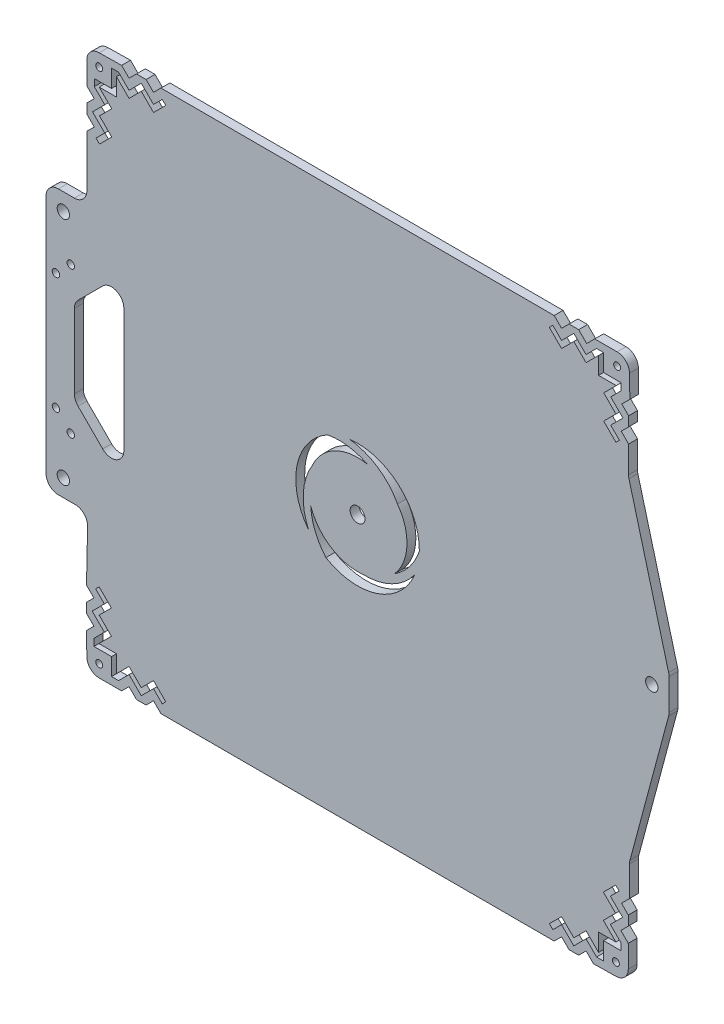
SolidWorks part; units mm, degrees
ref_plane "Front Plane" through (0, 0, 0) normal (0, 0, 1) x (1, 0, 0)
ref_plane "Top Plane" through (0, 0, 0) normal (0, 1, 0) x (1, 0, 0)
ref_plane "Right Plane" through (0, 0, 0) normal (1, 0, 0) x (0, 0, -1)
sketch "Model" plane through (0, 0, 0) normal (0, 0, 1) x (1, 0, 0)
  line L0 (-4, 125.6) -> (2.5, 125.6)
  line L1 (-4, 18.4) -> (2.8123, 18.4)
  line L2 (-9, 120.6) -> (-9, 23.4)
  line L3 (231.5, 82) -> (231.6, 82)
  line L4 (243, 74) -> (243, 65.6583)
  line L5 (231.5, 62) -> (231.6, 62)
  line L6 (243, 74) -> (243, 78.276)
  line L7 (242.9824, 79) -> (243, 79)
  line L8 (3.9228, 90.5355) -> (13.9228, 100.5355)
  line L9 (227, 4.6289) -> (227, -7.5294)
  line L10 (7.5, 151.5294) -> (7.5, 130.6)
  line L11 (7.5, 161.4289) -> (7.5, 157.5294)
  line L12 (7.5, 176.5) -> (7.5, 167.4289)
  line L13 (27.5711, 181.6421) -> (31.4706, 181.6421)
  line L14 (27.5711, -37.5) -> (31.4706, -37.5)
  line L15 (12.5, -37.5) -> (21.5711, -37.5)
  line L16 (7.3579, -17.4289) -> (7.3579, -13.5294)
  line L17 (226.5, -17.4289) -> (226.5, -13.5294)
  line L18 (226.5, -32.5) -> (226.5, -23.4289)
  line L19 (206.4289, -37.6421) -> (202.5294, -37.6421)
  line L20 (206.4289, 181.5) -> (202.5294, 181.5)
  line L21 (222, 181.5) -> (212.9289, 181.5)
  line L22 (226.6421, 161.4289) -> (226.6421, 157.5294)
  line L23 (14.7426, 154.5294) -> (9.7929, 159.4792)
  line L24 (14.7426, 164.4289) -> (9.7929, 159.4792)
  line L25 (17.5711, 164.4289) -> (12.6213, 159.4792)
  line L26 (17.5711, 154.5294) -> (12.6213, 159.4792)
  line L27 (17.5711, 164.4289) -> (12.5, 169.5)
  line L28 (14.7426, 164.4289) -> (10.5, 168.6716)
  line L29 (10.5, 168.6716) -> (10.5, 171.5)
  line L30 (10.5, 164.4289) -> (7.5, 161.4289)
  line L31 (10.5, 164.4289) -> (7.5, 167.4289)
  line L32 (10.5, 154.5294) -> (7.5, 151.5294)
  line L33 (10.5, 154.5294) -> (7.5, 157.5294)
  line L34 (34.4706, 174.3995) -> (29.5208, 179.3492)
  line L35 (24.5711, 174.3995) -> (29.5208, 179.3492)
  line L36 (24.5711, 171.5711) -> (29.5208, 176.5208)
  line L37 (34.4706, 171.5711) -> (29.5208, 176.5208)
  line L38 (24.5711, 171.5711) -> (19.5, 176.6421)
  line L39 (24.5711, 174.3995) -> (20.3284, 178.6421)
  line L40 (20.3284, 178.6421) -> (17.5, 178.6421)
  line L41 (24.5711, 178.6421) -> (27.5711, 181.6421)
  line L42 (24.5711, 178.6421) -> (21.5711, 181.6421)
  line L43 (34.4706, 178.6421) -> (37.4706, 181.6421)
  line L44 (34.4706, 178.6421) -> (31.4706, 181.6421)
  line L45 (17.5, 178.6421) -> (17.5, 171.5)
  line L46 (10.5, 171.5) -> (17.5, 171.5)
  line L47 (19.5, 176.6421) -> (19.5, 169.5)
  line L48 (12.5, 169.5) -> (19.5, 169.5)
  line L49 (21.5711, 181.6421) -> (12.5, 181.5)
  line L50 (34.4706, -30.2574) -> (29.5208, -35.2071)
  line L51 (24.5711, -30.2574) -> (29.5208, -35.2071)
  line L52 (24.5711, -27.4289) -> (29.5208, -32.3787)
  line L53 (34.4706, -27.4289) -> (29.5208, -32.3787)
  line L54 (24.5711, -27.4289) -> (19.5, -32.5)
  line L55 (24.5711, -30.2574) -> (20.3284, -34.5)
  line L56 (20.3284, -34.5) -> (17.5, -34.5)
  line L57 (24.5711, -34.5) -> (27.5711, -37.5)
  line L58 (24.5711, -34.5) -> (21.5711, -37.5)
  line L59 (34.4706, -34.5) -> (37.4706, -37.5)
  line L60 (34.4706, -34.5) -> (31.4706, -37.5)
  line L61 (14.6005, -10.5294) -> (9.6508, -15.4792)
  line L62 (14.6005, -20.4289) -> (9.6508, -15.4792)
  line L63 (17.4289, -20.4289) -> (12.4792, -15.4792)
  line L64 (17.4289, -10.5294) -> (12.4792, -15.4792)
  line L65 (17.4289, -20.4289) -> (12.3579, -25.5)
  line L66 (14.6005, -20.4289) -> (10.3579, -24.6716)
  line L67 (10.3579, -24.6716) -> (10.3579, -27.5)
  line L68 (10.3579, -20.4289) -> (7.3579, -17.4289)
  line L69 (10.3579, -20.4289) -> (7.3579, -23.4289)
  line L70 (10.3579, -10.5294) -> (7.3579, -7.5294)
  line L71 (10.3579, -10.5294) -> (7.3579, -13.5294)
  line L72 (10.3579, -27.5) -> (17.5, -27.5)
  line L73 (17.5, -34.5) -> (17.5, -27.5)
  line L74 (12.3579, -25.5) -> (19.5, -25.5)
  line L75 (19.5, -32.5) -> (19.5, -25.5)
  line L76 (7.3579, -23.4289) -> (7.5, -32.5)
  line L77 (219.2574, -10.5294) -> (224.2071, -15.4792)
  line L78 (219.2574, -20.4289) -> (224.2071, -15.4792)
  line L79 (216.4289, -20.4289) -> (221.3787, -15.4792)
  line L80 (216.4289, -10.5294) -> (221.3787, -15.4792)
  line L81 (216.4289, -20.4289) -> (221.5, -25.5)
  line L82 (219.2574, -20.4289) -> (223.5, -24.6716)
  line L83 (223.5, -24.6716) -> (223.5, -27.5)
  line L84 (223.5, -20.4289) -> (226.5, -17.4289)
  line L85 (223.5, -20.4289) -> (226.5, -23.4289)
  line L86 (223.75, -10.7794) -> (227, -7.5294)
  line L87 (223.75, -10.7794) -> (226.5, -13.5294)
  line L88 (199.5294, -30.3995) -> (204.4792, -35.3492)
  line L89 (209.4289, -30.3995) -> (204.4792, -35.3492)
  line L90 (209.4289, -27.5711) -> (204.4792, -32.5208)
  line L91 (199.5294, -27.5711) -> (204.4792, -32.5208)
  line L92 (209.4289, -27.5711) -> (214.5, -32.6421)
  line L93 (209.4289, -30.3995) -> (213.6716, -34.6421)
  line L94 (213.6716, -34.6421) -> (216.5, -34.6421)
  line L95 (209.4289, -34.6421) -> (206.4289, -37.6421)
  line L96 (209.4289, -34.6421) -> (212.4289, -37.6421)
  line L97 (199.5294, -34.6421) -> (196.5294, -37.6421)
  line L98 (199.5294, -34.6421) -> (202.5294, -37.6421)
  line L99 (216.5, -34.6421) -> (216.5, -27.5)
  line L100 (223.5, -27.5) -> (216.5, -27.5)
  line L101 (214.5, -32.6421) -> (214.5, -25.5)
  line L102 (221.5, -25.5) -> (214.5, -25.5)
  line L103 (212.4289, -37.6421) -> (221.5, -37.5)
  line L104 (199.5294, 174.2574) -> (204.4792, 179.2071)
  line L105 (209.4289, 174.2574) -> (204.4792, 179.2071)
  line L106 (209.4289, 171.4289) -> (204.4792, 176.3787)
  line L107 (199.5294, 171.4289) -> (204.4792, 176.3787)
  line L108 (209.4289, 171.4289) -> (214.5, 176.5)
  line L109 (209.4289, 174.2574) -> (213.6716, 178.5)
  line L110 (213.6716, 178.5) -> (216.5, 178.5)
  line L111 (209.6789, 178.25) -> (206.4289, 181.5)
  line L112 (209.6789, 178.25) -> (212.9289, 181.5)
  line L113 (199.5294, 178.5) -> (196.5294, 181.5)
  line L114 (199.5294, 178.5) -> (202.5294, 181.5)
  line L115 (219.3995, 154.5294) -> (224.3492, 159.4792)
  line L116 (219.3995, 164.4289) -> (224.3492, 159.4792)
  line L117 (216.5711, 164.4289) -> (221.5208, 159.4792)
  line L118 (216.5711, 154.5294) -> (221.5208, 159.4792)
  line L119 (216.5711, 164.4289) -> (221.6421, 169.5)
  line L120 (219.3995, 164.4289) -> (223.6421, 168.6716)
  line L121 (223.6421, 168.6716) -> (223.6421, 171.5)
  line L122 (223.8921, 164.1789) -> (226.6421, 161.4289)
  line L123 (223.8921, 164.1789) -> (227.1421, 167.4289)
  line L124 (223.6421, 154.5294) -> (226.6421, 151.5294)
  line L125 (223.6421, 154.5294) -> (226.6421, 157.5294)
  line L126 (223.6421, 171.5) -> (216.5, 171.5)
  line L127 (216.5, 178.5) -> (216.5, 171.5)
  line L128 (221.6421, 169.5) -> (214.5, 169.5)
  line L129 (214.5, 176.5) -> (214.5, 169.5)
  line L130 (227.1421, 167.4289) -> (227, 176.5)
  line L131 (37.4706, 181.6421) -> (196.5294, 181.5)
  line L132 (226.6421, 151.5294) -> (226.6184, 140.7406)
  line L133 (227.1704, 5.923) -> (242.8296, 64.3642)
  line L134 (196.5294, -37.6421) -> (37.4706, -37.5)
  line L135 (7.3579, -7.5294) -> (7.8111, 13.2912)
  line L136 (14.6005, -10.5294) -> (11.065, -6.9939)
  line L137 (12.4792, -5.5797) -> (11.065, -6.9939)
  line L138 (17.4289, -10.5294) -> (12.4792, -5.5797)
  line L139 (34.4706, -30.2574) -> (38.0061, -33.7929)
  line L140 (39.4203, -32.3787) -> (38.0061, -33.7929)
  line L141 (34.4706, -27.4289) -> (39.4203, -32.3787)
  line L142 (216.4289, -10.5294) -> (221.3787, -5.5797)
  line L143 (221.3787, -5.5797) -> (222.7929, -6.9939)
  line L144 (219.2574, -10.5294) -> (222.7929, -6.9939)
  line L145 (199.5294, -27.5711) -> (194.5797, -32.5208)
  line L146 (194.5797, -32.5208) -> (195.9939, -33.935)
  line L147 (199.5294, -30.3995) -> (195.9939, -33.935)
  line L148 (199.5294, 174.2574) -> (195.9939, 177.7929)
  line L149 (194.5797, 176.3787) -> (195.9939, 177.7929)
  line L150 (199.5294, 171.4289) -> (194.5797, 176.3787)
  line L151 (219.3995, 154.5294) -> (222.935, 150.9939)
  line L152 (221.5208, 149.5797) -> (222.935, 150.9939)
  line L153 (216.5711, 154.5294) -> (221.5208, 149.5797)
  line L154 (34.4706, 174.3995) -> (38.0061, 177.935)
  line L155 (39.4203, 176.5208) -> (38.0061, 177.935)
  line L156 (34.4706, 171.5711) -> (39.4203, 176.5208)
  line L157 (14.7426, 154.5294) -> (11.2071, 150.9939)
  line L158 (12.6213, 149.5797) -> (11.2071, 150.9939)
  line L159 (17.5711, 154.5294) -> (12.6213, 149.5797)
  line L160 (226.7887, 139.4355) -> (242.8296, 79.5701)
  line L161 (3.9228, 53.4645) -> (13.9228, 43.4645)
  line L164 (22.4584, 47) -> (22.4584, 97)
  line L166 (2.4584, 57) -> (2.4584, 87)
  arc A0 (-4, 18.4) -> (-9, 23.4) centre (-4, 23.4) cw
  arc A1 (7.8111, 13.2912) -> (2.8123, 18.4) centre (2.8123, 13.4) ccw
  arc A2 (-9, 120.6) -> (-4, 125.6) centre (-4, 120.6) cw
  arc A3 (226.7887, 139.4355) -> (226.6184, 140.7406) centre (231.6184, 140.7296) cw
  arc A4 (12.5, 181.5) -> (7.5, 176.5) centre (12.5, 176.5) ccw
  arc A5 (243, 78.276) -> (242.8296, 79.5701) centre (238, 78.276) ccw
  arc A6 (242.8296, 64.3642) -> (243, 65.6583) centre (238, 65.6583) ccw
  arc A7 (227, 4.6289) -> (227.1704, 5.923) centre (232, 4.6289) cw
  arc A8 (7.5, 130.6) -> (2.5, 125.6) centre (2.5, 130.6) cw
  arc A9 (7.5, -32.5) -> (12.5, -37.5) centre (12.5, -32.5) ccw
  arc A10 (221.5, -37.5) -> (226.5, -32.5) centre (221.5, -32.5) ccw
  arc A11 (227, 176.5) -> (222, 181.5) centre (222, 176.5) ccw
  circle A12 centre (-2, 118.6) radius 2.5
  circle A13 centre (-2, 25.4) radius 2.5
  circle A14 centre (236, 72) radius 2.5
  circle A15 centre (12.5, 176.5) radius 1.4
  circle A16 centre (117, 72) radius 3
  circle A17 centre (-5, 95.6) radius 1.5
  circle A18 centre (1, 101.6) radius 1.5
  arc A19 (98.7307, 80.1384) -> (97.2089, 56.7254) centre (120, 67) ccw
  arc A20 (98.0368, 65.6442) -> (104.1919, 50.5302) centre (123, 67) ccw
  arc A21 (119.0865, 52.1091) -> (140.1237, 62.4978) centre (119.8301, 77.0981) ccw
  arc A22 (131.9859, 58.7553) -> (141.9974, 71.6427) centre (118.3301, 79.6962) ccw
  arc A23 (133.1827, 83.7524) -> (113.6673, 96.7769) centre (111.1699, 71.9019) ccw
  arc A24 (120.9773, 91.6005) -> (104.8107, 93.8271) centre (109.6699, 69.3038) ccw
  arc A25 (141.9974, 71.6427) -> (113.6673, 96.7769) centre (117, 72) ccw
  arc A26 (104.1919, 50.5302) -> (140.1237, 62.4978) centre (117, 72) ccw
  arc A27 (104.8107, 93.8271) -> (97.2089, 56.7254) centre (117, 72) ccw
  arc A28 (120.9773, 91.6005) -> (98.7307, 80.1384) centre (117, 72) ccw
  arc A29 (131.9859, 58.7553) -> (133.1827, 83.7524) centre (117, 72) ccw
  arc A30 (98.0368, 65.6442) -> (119.0865, 52.1091) centre (117, 72) ccw
  circle A31 centre (12.5, -32.5) radius 1.4
  circle A32 centre (221.5, -32.5) radius 1.4
  circle A33 centre (222, 176.5) radius 1.4
  circle A34 centre (-5, 48.4) radius 1.5
  circle A35 centre (1, 42.4) radius 1.5
  arc A36 (2.4584, 57) -> (3.9228, 53.4645) centre (7.4584, 57) ccw
  arc A37 (3.9228, 90.5355) -> (2.4584, 87) centre (7.4584, 87) ccw
  arc A38 (13.9228, 100.5355) -> (22.4584, 97) centre (17.4584, 97) cw
  arc A39 (22.4584, 47) -> (13.9228, 43.4645) centre (17.4584, 47) cw
  point P8 (226.4824, 79)
  point P10 (226, 65)
  point P76 (2.4584, 52)
  point P231 (2.4584, 92)
  point P234 (22.4584, 92)
  dimension "D2" = 119
  dimension "D3" = 119
  dimension "D4" = 30
  dimension "D5" = 30
  dimension "D6" = 7
  dimension "D7" = 5
  dimension "D8" = 75
  dimension "D9" = 7
  dimension "D10" = 7
  dimension "D11" = 7
  dimension "D12" = 5
  dimension "D13" = 5
  dimension "D14" = 5
  dimension "D15" = 5
  dimension "D16" = 15
  dimension "D17" = 5
  dimension "D18" = 5
  dimension "D19" = 5
  dimension "D20" = 20
  dimension "D25" = 5
  dimension "D26" = 5
  dimension "D22" = 5
  dimension "D1" = 119
  dimension "D21" = 40
  dimension "D23" = 24
  dimension "D24" = 24
extrude "Boss-Extrude1" add sketch "Model" along normal blind 3.6 contours L130 A11 L21 L112 L111 L20 L114 L113 L131 L43 L44 L13 L41 L42 L49 A4 L12 L31 L30 L11 L33 L32 L10 A8 L0 A2 L2 A0 L1 A1 L135 L70 L71 L16 L68 L69 L76 A9 L15 L58 L57 L14 L60 L59 L134 L97 L98 L19 L95 L96 L103
